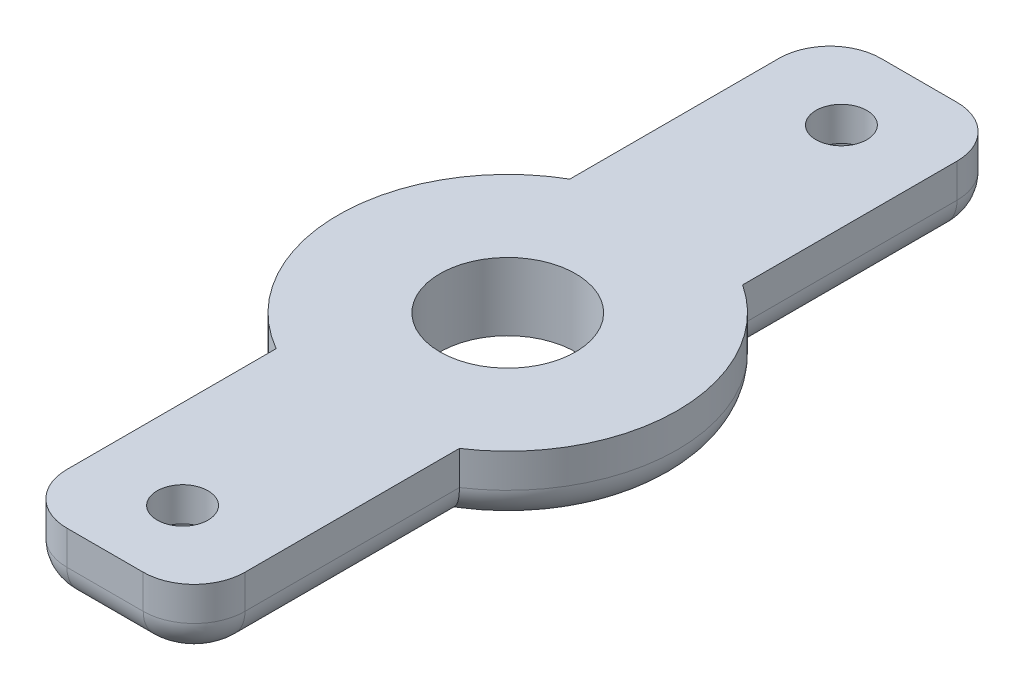
SolidWorks part; units mm, degrees
ref_plane "Front Plane" through (0, 0, 0) normal (0, 0, 1) x (1, 0, 0)
ref_plane "Top Plane" through (0, 0, 0) normal (0, 1, 0) x (1, 0, 0)
ref_plane "Right Plane" through (0, 0, 0) normal (1, 0, 0) x (0, 0, -1)
sketch "Sketch1" plane through (0, 0, 0) normal (0, 1, 0) x (1, 0, 0)
  line L0 (5.25, -21) -> (5.25, 21)
  line L1 (2.25, 24) -> (-2.25, 24)
  line L2 (-5.25, 21) -> (-5.25, -21)
  line L3 (-2.25, -24) -> (2.25, -24)
  circle A0 centre (-0.25, 0) radius 4
  arc A1 (2.25, -24) -> (5.25, -21) centre (2.25, -21) ccw
  arc A2 (5.25, 21) -> (2.25, 24) centre (2.25, 21) ccw
  arc A3 (-2.25, 24) -> (-5.25, 21) centre (-2.25, 21) ccw
  arc A4 (-5.25, -21) -> (-2.25, -24) centre (-2.25, -21) ccw
extrude "Boss-Extrude1" add sketch "Sketch1" along normal blind 4
sketch "Sketch2" plane through (0, 0, 0) normal (0, -1, 0) x (1, 0, 0)
  line L0 (0, 0) -> (-5.25, 0) construction
  line L1 (-5.25, -21) -> (-5.25, 21) construction
  circle A4 centre (0, 19.4285) radius 1.5
  circle A5 centre (0, -19.4285) radius 1.5
extrude "Cut-Extrude1" cut sketch "Sketch2" against normal blind 10
sketch "Sketch3" plane through (0, 0, 0) normal (0, -1, 0) x (1, 0, 0)
  circle A0 centre (0, 19.4285) radius 2.5
  circle A1 centre (0, -19.4285) radius 2.5
  dimension "D1" = 5
  dimension "D2" = 5
extrude "Cut-Extrude2" cut sketch "Sketch3" against normal blind 2
sketch "Sketch4" plane through (0, 0, 0) normal (0, -1, 0) x (1, 0, 0)
  circle A0 centre (-0.25, 0) radius 10
  circle A1 centre (-0.25, 0) radius 4 construction
  circle A2 centre (-0.25, 0) radius 4
extrude "Boss-Extrude3" add sketch "Sketch4" against normal blind 4
fillet "Fillet1" radius 2 12 edges at (5.25, 0, -14.6758) (4.3713, 0, -23.1213) (0, 0, -24) (-4.3713, 0, -23.1213) (5.25, 0, 14.6758) (4.3713, 0, 23.1213) (0, 0, 24) (-4.3713, 0, 23.1213) (-5.25, 0, -14.8301) (9.75, 0, 0) (-5.25, 0, 14.8301) (-10.25, 0, 0)
